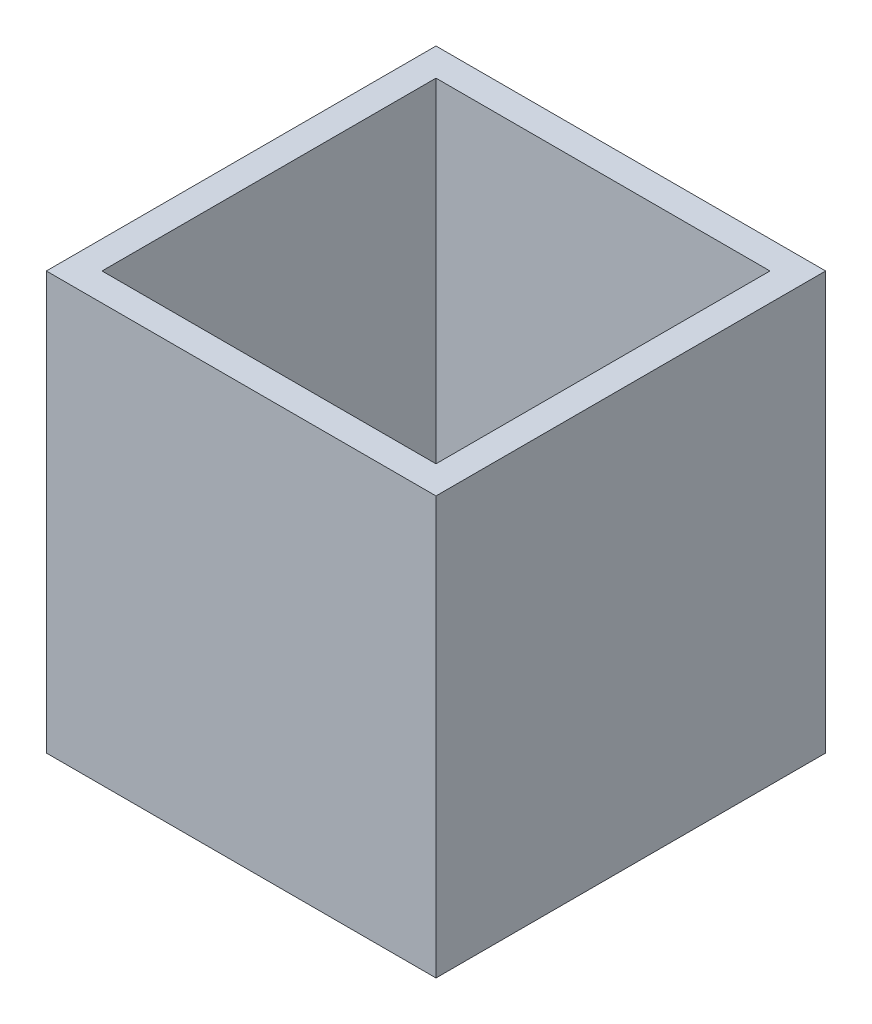
SolidWorks part; units mm, degrees
ref_plane "Спереди" through (0, 0, 0) normal (0, 0, 1) x (1, 0, 0)
ref_plane "Сверху" through (0, 0, 0) normal (0, 1, 0) x (1, 0, 0)
ref_plane "Справа" through (0, 0, 0) normal (1, 0, 0) x (0, 0, -1)
sketch "Эскиз1" plane through (0, 0, 0) normal (0, 1, 0) x (1, 0, 0)
  line L1 (-14, 14) -> (14, 14)
  line L2 (-14, 14) -> (-14, -14)
  line L3 (-14, -14) -> (14, -14)
  line L4 (14, 14) -> (14, -14)
  line L5 (-14, 14) -> (14, -14) construction
  line L6 (-14, -14) -> (14, 14) construction
  point P0 (0, 0)
extrude "Вытянуть-Тонкостенный1" add sketch "Эскиз1" along normal blind 30 thin
